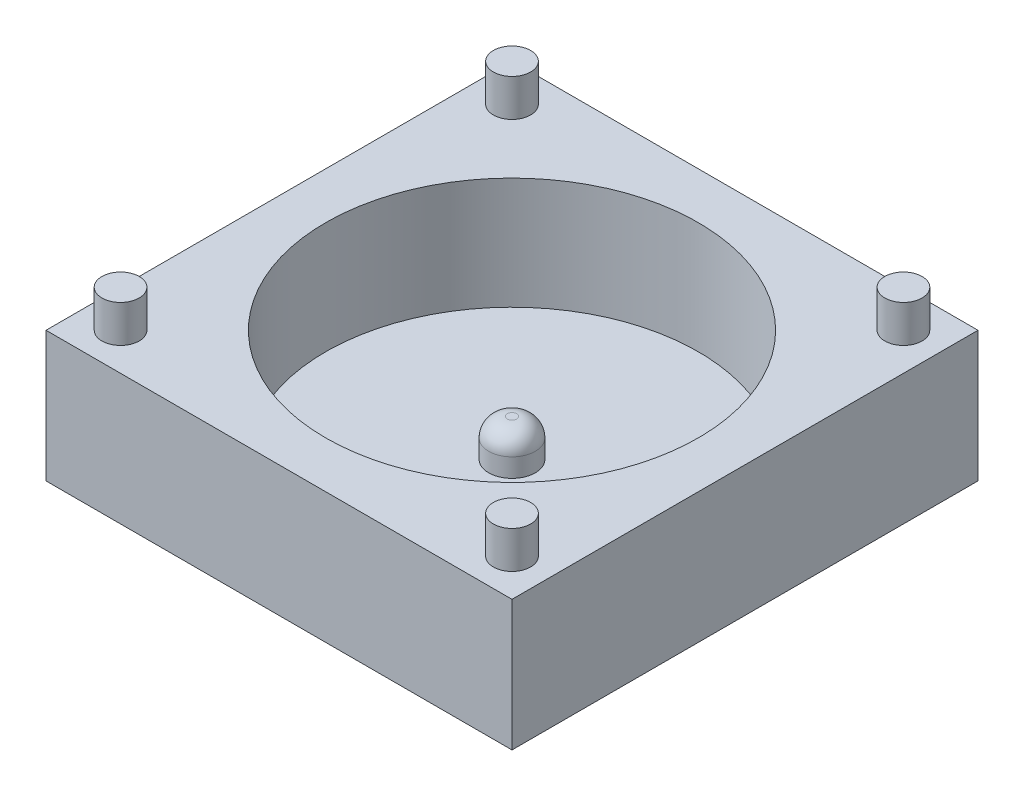
SolidWorks part; units mm, degrees
ref_plane "Front Plane" through (0, 0, 0) normal (0, 0, 1) x (1, 0, 0)
ref_plane "Top Plane" through (0, 0, 0) normal (0, 1, 0) x (1, 0, 0)
ref_plane "Right Plane" through (0, 0, 0) normal (1, 0, 0) x (0, 0, -1)
sketch "Sketch1" plane through (0, 0, 0) normal (0, 1, 0) x (1, 0, 0)
  line L1 (-12.5, -12.5) -> (12.5, -12.5)
  line L2 (-12.5, -12.5) -> (-12.5, 12.5)
  line L3 (-12.5, 12.5) -> (12.5, 12.5)
  line L4 (12.5, -12.5) -> (12.5, 12.5)
  line L5 (-12.5, -12.5) -> (12.5, 12.5) construction
  line L6 (-12.5, 12.5) -> (12.5, -12.5) construction
  point P0 (0, 0)
  dimension "D1" = 25
  dimension "D2" = 25
extrude "Boss-Extrude1" add sketch "Sketch1" along normal blind 7
sketch "Sketch2" plane through (0, 7, 0) normal (0, 1, 0) x (1, 0, 0)
  circle A0 centre (0, 0) radius 10
  dimension "D1" = 20
extrude "Cut-Extrude1" cut sketch "Sketch2" against normal blind 6
sketch "Sketch3" plane through (0, 1, 0) normal (0, 1, 0) x (1, 0, 0)
  circle A0 centre (0, 0) radius 1.25
  dimension "D1" = 2.5
extrude "Boss-Extrude2" add sketch "Sketch3" along normal blind 2
fillet "Fillet1" radius 1 1 edges at (0, 3, 1.25)
sketch "Sketch4" plane through (0, 7, 0) normal (0, 1, 0) x (1, 0, 0)
  line L0 (-12.5, -12.5) -> (12.5, -12.5) construction
  line L1 (-12.5, 12.5) -> (-12.5, -12.5) construction
  line L2 (12.5, 12.5) -> (-12.5, 12.5) construction
  line L3 (12.5, -12.5) -> (12.5, 12.5) construction
  circle A0 centre (-10.5, 10.5) radius 1
  circle A1 centre (10.5, 10.5) radius 1
  circle A2 centre (10.5, -10.5) radius 1
  circle A3 centre (-10.5, -10.5) radius 1
  dimension "D1" = 2
  dimension "D4" = 2
  dimension "D7" = 2
  dimension "D10" = 2
  dimension "D2" = 2
  dimension "D3" = 2
  dimension "D5" = 2
  dimension "D6" = 2
  dimension "D8" = 2
  dimension "D9" = 2
  dimension "D11" = 2
  dimension "D12" = 2
extrude "Boss-Extrude3" add sketch "Sketch4" along normal blind 2
